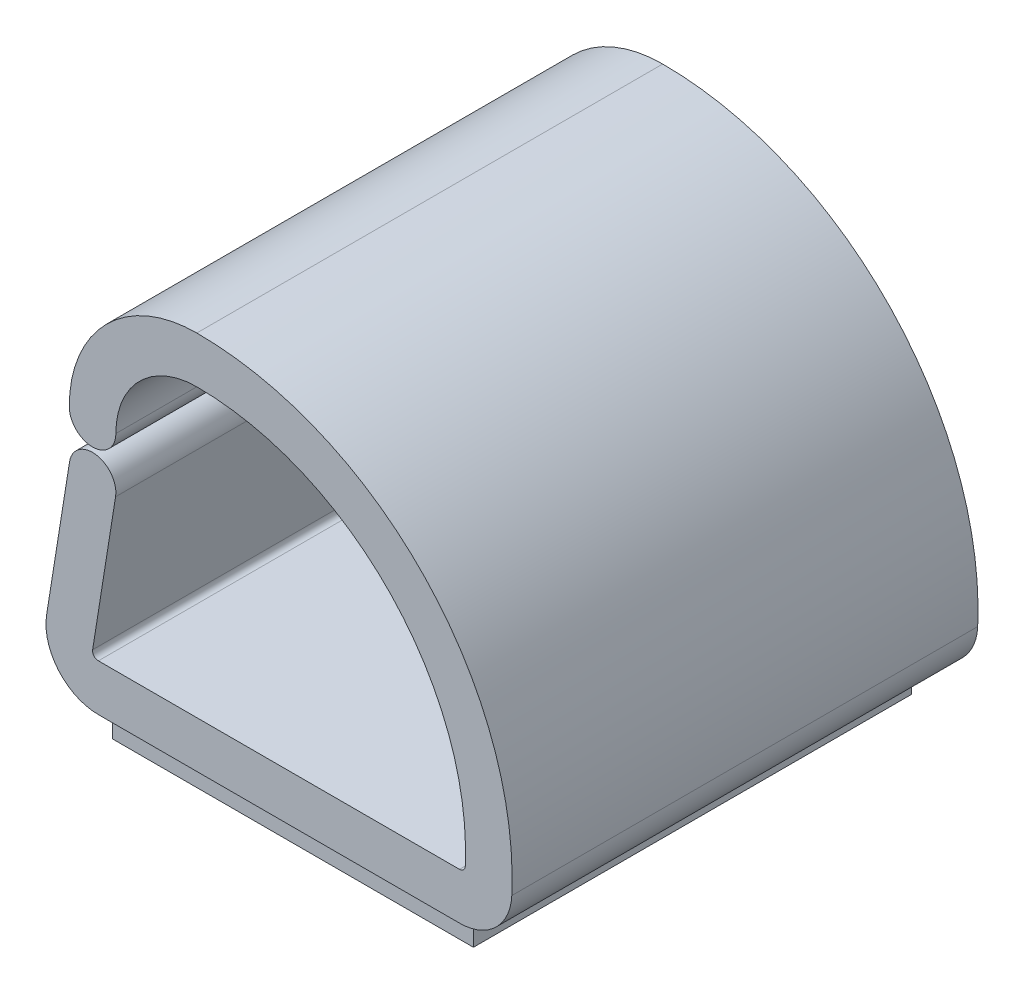
SolidWorks part; units mm, degrees
ref_plane "Front Plane" through (0, 0, 0) normal (0, 0, 1) x (1, 0, 0)
ref_plane "Top Plane" through (0, 0, 0) normal (0, 1, 0) x (1, 0, 0)
ref_plane "Right Plane" through (0, 0, 0) normal (1, 0, 0) x (0, 0, -1)
sketch "Sketch1" plane through (0, 0, 0) normal (0, 1, 0) x (1, 0, 0)
  line L1 (-6.35, -6.35) -> (6.35, -6.35)
  line L2 (-6.35, -6.35) -> (-6.35, 6.35)
  line L3 (-6.35, 6.35) -> (6.35, 6.35)
  line L4 (6.35, -6.35) -> (6.35, 6.35)
  line L5 (-6.35, -6.35) -> (6.35, 6.35) construction
  line L6 (-6.35, 6.35) -> (6.35, -6.35) construction
  point P0 (0, 0)
  dimension "Length" = 12.7
  dimension "Width" = 12.7
sketch "Sketch2" plane through (0, 0, 0) normal (0, 0, 1) x (1, 0, 0)
  line L0 (0, -0.762) -> (0, 10.3505) construction
  dimension "Height" = 11.1125
  dimension "D1" = 0.762
sketch "Sketch5" plane through (0, 0, 0) normal (0, 0, 1) x (1, 0, 0)
  line L1 (0, -0.762) -> (0, 10.3505) construction
  line L2 (-6.35, 0) -> (-6.35, 10.3505) construction
  line L3 (6.35, 0) -> (6.35, 10.3505) construction
  line L4 (-4.9213, 0) -> (4.9212, 0)
  line L5 (-6.3322, 1.6536) -> (-5.7071, 5.5768)
  line L6 (-4.4529, 5.377) -> (-5.078, 1.4537)
  line L8 (-4.9213, 1.27) -> (4.9212, 1.27)
  line L9 (-6.35, 6.1119) -> (6.35, 6.1119) construction
  line L10 (-6.35, 10.3505) -> (6.35, 10.3505) construction
  line L11 (-6.35, 6.2389) -> (6.35, 6.2389) construction
  arc A0 (6.3485, 1.3638) -> (-2.2384, 10.3505) centre (-2.2384, 1.7547) ccw
  arc A1 (-2.2384, 10.3505) -> (-5.715, 6.8739) centre (-2.2384, 6.8739) ccw
  arc A2 (-4.9213, 0) -> (-6.3322, 1.6536) centre (-4.9213, 1.4288) cw
  arc A3 (4.9212, 0) -> (6.3485, 1.3638) centre (4.9212, 1.4288) ccw
  arc A4 (-5.7071, 5.5768) -> (-4.4529, 5.377) centre (-5.08, 5.4769) cw
  arc A5 (4.9212, 1.27) -> (5.0798, 1.4215) centre (4.9212, 1.4288) ccw
  arc A6 (5.0798, 1.4215) -> (-2.2384, 9.0805) centre (-2.2384, 1.7547) ccw
  arc A7 (-4.9213, 1.27) -> (-5.078, 1.4537) centre (-4.9213, 1.4288) cw
  arc A8 (-2.2384, 9.0805) -> (-4.445, 6.8739) centre (-2.2384, 6.8739) ccw
  arc A9 (-4.445, 6.8739) -> (-5.715, 6.8739) centre (-5.08, 6.8739) cw
  point P0 (0, 0.635)
  dimension "D4" = 0.1588
  dimension "Thickness" = 1.27
  dimension "D3" = 6.1119
  dimension "D1" = 1.27
  dimension "D5" = 0.127
extrude "Boss-Extrude3" add sketch "Sketch5" along normal up to vertex (6.35 mm away) and the other way up to vertex (6.35 mm away) up to point (-6.35, 0, 6.35) other way up to point (-6.35, 0, -6.35)
sketch "Sketch6" plane through (0, 0, 0) normal (0, -1, 0) x (1, 0, 0)
  line L0 (-4.9213, 6.35) -> (-4.9213, -6.35) construction
  line L1 (4.9212, 6.35) -> (4.9212, -6.35) construction
  line L2 (-6.35, 6.35) -> (6.35, 6.35) construction
  line L3 (-6.35, -6.35) -> (6.35, -6.35) construction
  line L4 (-4.9213, 6.35) -> (-4.9213, -6.35)
  line L5 (-4.9213, -6.35) -> (4.9212, -6.35)
  line L6 (4.9212, -6.35) -> (4.9212, 6.35)
  line L7 (4.9212, 6.35) -> (-4.9213, 6.35)
  line L8 (-4.9213, 5.969) -> (-4.9213, -5.969)
  line L9 (-4.9213, -5.969) -> (4.9212, -5.969)
  line L10 (4.9212, -5.969) -> (4.9212, 5.969)
  line L11 (4.9212, 5.969) -> (-4.9213, 5.969)
  dimension "D2" = 0.381
  dimension "D3" = 0.381
  dimension "D1" = 0
extrude "Boss-Extrude4" add sketch "Sketch6" along normal up to vertex (0.762 mm away) up to point (0, -0.762, 0)
sketch3d "3DSketch1"
  line L0 (1.8793, 3.491, -6.8073) -> (1.8793, 3.491, 6.7627) construction
  line L1 (-1.8897, 6.5454, -6.792) -> (-1.8897, 6.5454, 6.9429) construction
  line L2 (-2.6008, 2.8831, -6.8335) -> (-2.6008, 2.8831, 6.6874) construction
equation "\"D3@Sketch5\"=\"Height@Sketch2\"*.55"
equation "\"D1@Sketch5\"=\"Length@Sketch1\"*.1"
equation "\"D4@Sketch5\"=\"Thickness@Sketch5\"/8"
